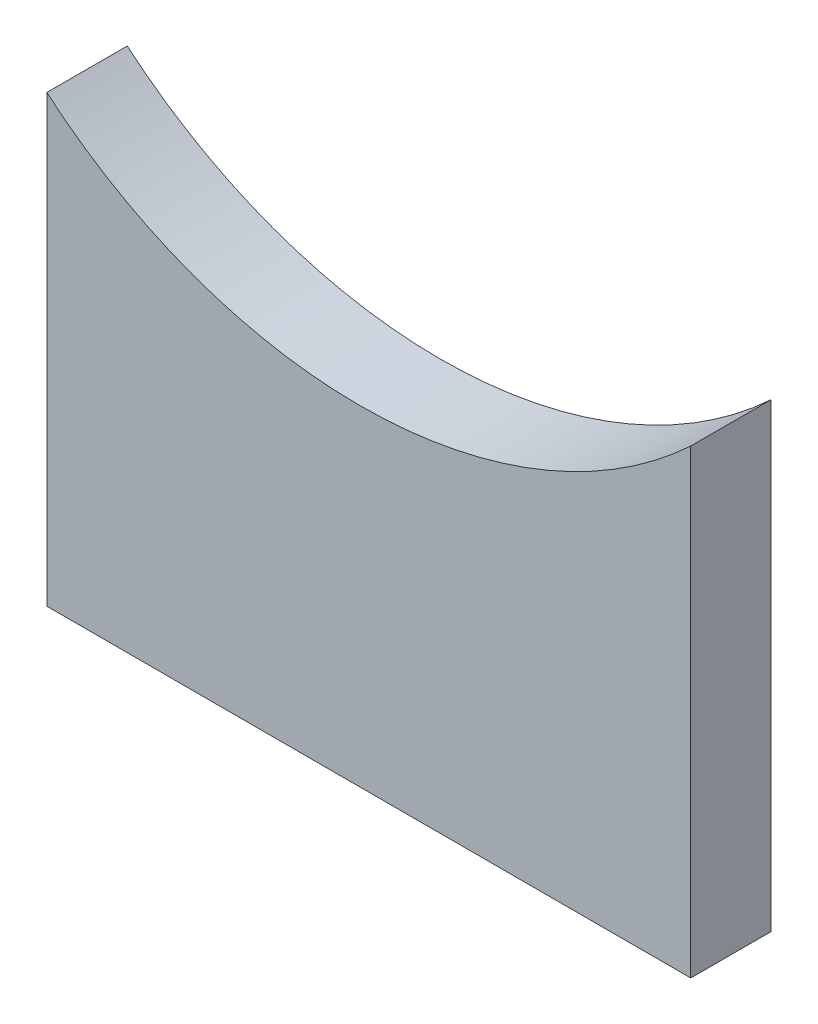
SolidWorks part; units mm, degrees
material "1.7218 (25CrMo4)"
ref_plane "Płaszczyzna XY" through (0, 0, 0) normal (0, 0, 1) x (1, 0, 0)
ref_plane "Płaszczyzna XZ" through (0, 0, 0) normal (0, 1, 0) x (1, 0, 0)
ref_plane "Płaszczyzna YZ" through (0, 0, 0) normal (1, 0, 0) x (0, 0, -1)
sketch "Szkic1" plane through (0, 0, 0) normal (0, 0, 1) x (1, 0, 0)
  line L0 (0, 55.3307) -> (0, 0) construction
  line L1 (0, 0) -> (45.491, 0) construction
  line L2 (0, 31.8557) -> (16, 31.8557)
  line L3 (16, 31.8557) -> (16, 26.1745)
  line L5 (0, 31.8557) -> (0, 0)
  line L6 (16, 0) -> (16, 26.1745)
  line L7 (0, 0) -> (16, 0)
  line L8 (0, 31.8557) -> (0, 0)
  line L9 (16, 0) -> (16, 26.1745)
  line L10 (0, 0) -> (16, 0)
  spline S1 degree 3 poles (16, 26.1745) (9.1813, 23.4108) (2.9905, 26.3813) (0, 31.8557) knots 0.071166 0.071166 0.071166 0.071166 0.277144 0.277144 0.277144 0.277144 weights 0.505895 0.476075 0.559394 0.755852
  dimension "D1" = 0
extrude "Dodanie-wyciągnięcie1" add sketch "Szkic1" along normal blind 2
sketch "Szkic2" plane through (0, 0, 2) normal (0, 0, 1) x (1, 0, 0)
  line L0 (0, 5) -> (16, 5)
  line L4 (16, 0) -> (16, 31.8557)
  line L5 (0, 31.8557) -> (0, 0)
  line L6 (0, 0) -> (16, 0)
  line L7 (16, 0) -> (16, 31.8557)
  line L8 (0, 31.8557) -> (0, 0)
  line L9 (0, 0) -> (16, 0)
  line L11 (16, 31.8557) -> (0, 31.8557)
  line L12 (16, 31.8557) -> (0, 31.8557)
  line M18 (16, 0) -> (16, 31.8557)
  line M20 (0, 31.8557) -> (0, 0)
  line M21 (0, 0) -> (16, 0)
  dimension "D2" = 5
  dimension "D1" = 0
extrude "Wytnij-wyciągnięcie1" cut sketch "Szkic2" against normal blind 5 contours L0 M20 M21 M18
sketch "Szkic6" plane through (0, 0, 0) normal (0, 0, -1) x (-1, 0, 0)
  line L0 (0, 31.8557) -> (-16, 31.8557)
  line L1 (-16, 31.8557) -> (-16, 18.7509)
  line L2 (-16, 5) -> (-16, 31.8557) construction
  line L3 (0, 31.8557) -> (0, 18.4279)
  line L4 (0, 31.8557) -> (0, 5) construction
  arc A1 (0, 18.4279) -> (-16, 18.7509) centre (-7.8139, 27.8085) cw
  dimension "D1" = 12.2087
  dimension "D2" = 7.8139
extrude "Wytnij-wyciągnięcie2" cut sketch "Szkic6" against normal blind 10
sketch "Szkic8" plane through (0, 0, 0) normal (0, 0, -1) x (-1, 0, 0)
  line L0 (-16, 18.7509) -> (-16, 16.4463)
  line L1 (-16, 5) -> (-16, 18.7509) construction
  line L2 (0, 18.4279) -> (0, 16.0536)
  line L3 (0, 18.4279) -> (0, 5) construction
  line L4 (0, 18.4279) -> (-16, 18.7509)
  arc A0 (0, 16.0536) -> (-16, 16.4463) centre (-7.7789, 25.2581) cw
  dimension "D1" = 12.0513
extrude "Wytnij-wyciągnięcie3" cut sketch "Szkic8" against normal blind 10
